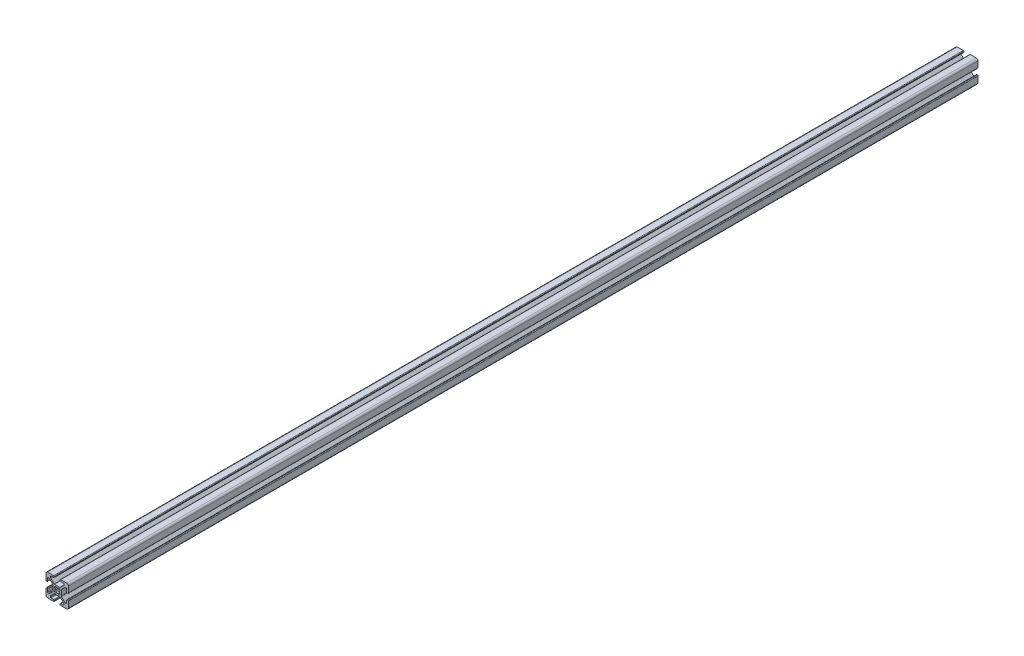
SolidWorks part; units mm, degrees
material "6063-T6"
ref_plane "Front Plane" through (0, 0, 0) normal (0, 0, 1) x (1, 0, 0)
ref_plane "Top Plane" through (0, 0, 0) normal (0, 1, 0) x (1, 0, 0)
ref_plane "Right Plane" through (0, 0, 0) normal (1, 0, 0) x (0, 0, -1)
sketch "Sketch1" plane through (0, 0, 0) normal (0, 0, 1) x (1, 0, 0)
  line L0 (9.492, 2.63) -> (9.008, 2.63)
  line L1 (8.5, 3.138) -> (8.5, 5.487)
  line L2 (10, 3.138) -> (10, 8.5)
  line L3 (3.655, -2.3839) -> (3.655, 2.3839)
  line L4 (7.2661, 5.995) -> (7.992, 5.995)
  line L5 (6.9069, 5.8462) -> (3.8038, 2.7431)
  line L6 (9.492, -2.63) -> (9.008, -2.63)
  line L7 (10, -3.138) -> (10, -8.5)
  line L8 (8.5, -3.138) -> (8.5, -5.487)
  line L9 (7.2661, -5.995) -> (7.992, -5.995)
  line L10 (6.9069, -5.8462) -> (3.8038, -2.7431)
  line L11 (2.1249, -2.3045) -> (2.3045, -2.1249)
  line L12 (-2.63, 9.492) -> (-2.63, 9.008)
  line L13 (-3.138, 10) -> (-8.5, 10)
  line L14 (-3.138, 8.5) -> (-5.487, 8.5)
  line L15 (2.3839, 3.655) -> (-2.3839, 3.655)
  line L16 (-5.995, 7.2661) -> (-5.995, 7.992)
  line L17 (-5.8462, 6.9069) -> (-2.7431, 3.8038)
  line L18 (2.63, 9.492) -> (2.63, 9.008)
  line L19 (3.138, 10) -> (8.5, 10)
  line L20 (3.138, 8.5) -> (5.487, 8.5)
  line L21 (5.995, 7.2661) -> (5.995, 7.992)
  line L22 (5.8462, 6.9069) -> (2.7431, 3.8038)
  line L23 (2.3045, 2.1249) -> (2.1249, 2.3045)
  line L24 (-9.492, -2.63) -> (-9.008, -2.63)
  line L25 (-10, -3.138) -> (-10, -8.5)
  line L26 (-8.5, -3.138) -> (-8.5, -5.487)
  line L27 (-3.655, 2.3839) -> (-3.655, -2.3839)
  line L28 (-7.2661, -5.995) -> (-7.992, -5.995)
  line L29 (-6.9069, -5.8462) -> (-3.8038, -2.7431)
  line L30 (-9.492, 2.63) -> (-9.008, 2.63)
  line L31 (-10, 3.138) -> (-10, 8.5)
  line L32 (-8.5, 3.138) -> (-8.5, 5.487)
  line L33 (-7.2661, 5.995) -> (-7.992, 5.995)
  line L34 (-6.9069, 5.8462) -> (-3.8038, 2.7431)
  line L35 (-2.1249, 2.3045) -> (-2.3045, 2.1249)
  line L36 (2.63, -9.492) -> (2.63, -9.008)
  line L37 (3.138, -10) -> (8.5, -10)
  line L38 (3.138, -8.5) -> (5.487, -8.5)
  line L39 (-2.3839, -3.655) -> (2.3839, -3.655)
  line L40 (5.995, -7.2661) -> (5.995, -7.992)
  line L41 (5.8462, -6.9069) -> (2.7431, -3.8038)
  line L42 (-2.63, -9.492) -> (-2.63, -9.008)
  line L43 (-3.138, -10) -> (-8.5, -10)
  line L44 (-3.138, -8.5) -> (-5.487, -8.5)
  line L45 (-5.995, -7.2661) -> (-5.995, -7.992)
  line L46 (-5.8462, -6.9069) -> (-2.7431, -3.8038)
  line L47 (-2.3045, -2.1249) -> (-2.1249, -2.3045)
  arc A0 (-0.804, -1.9351) -> (0.804, -1.9351) centre (0, 0) ccw
  arc A1 (8.5, 5.487) -> (7.992, 5.995) centre (7.992, 5.487) ccw
  arc A2 (7.2661, 5.995) -> (6.9069, 5.8462) centre (7.2661, 5.487) ccw
  arc A3 (3.8038, 2.7431) -> (3.655, 2.3839) centre (4.163, 2.3839) ccw
  arc A4 (3.655, -2.3839) -> (3.8038, -2.7431) centre (4.163, -2.3839) ccw
  arc A5 (6.9069, -5.8462) -> (7.2661, -5.995) centre (7.2661, -5.487) ccw
  arc A6 (7.992, -5.995) -> (8.5, -5.487) centre (7.992, -5.487) ccw
  arc A7 (9.008, -2.63) -> (8.5, -3.138) centre (9.008, -3.138) ccw
  arc A8 (10, -3.138) -> (9.492, -2.63) centre (9.492, -3.138) ccw
  arc A9 (9.492, 2.63) -> (10, 3.138) centre (9.492, 3.138) ccw
  arc A10 (8.5, 3.138) -> (9.008, 2.63) centre (9.008, 3.138) ccw
  arc A11 (0.804, -1.9351) -> (2.1249, -2.3045) centre (1.5684, -1.748) ccw
  arc A12 (2.3045, -2.1249) -> (1.9351, -0.804) centre (1.748, -1.5684) ccw
  arc A13 (-2.63, 9.492) -> (-3.138, 10) centre (-3.138, 9.492) ccw
  arc A14 (-3.138, 8.5) -> (-2.63, 9.008) centre (-3.138, 9.008) ccw
  arc A15 (1.9351, -0.804) -> (1.9351, 0.804) centre (0, 0) ccw
  arc A16 (-2.7431, 3.8038) -> (-2.3839, 3.655) centre (-2.3839, 4.163) ccw
  arc A17 (-5.487, 8.5) -> (-5.995, 7.992) centre (-5.487, 7.992) ccw
  arc A18 (-5.995, 7.2661) -> (-5.8462, 6.9069) centre (-5.487, 7.2661) ccw
  arc A19 (2.63, 9.008) -> (3.138, 8.5) centre (3.138, 9.008) ccw
  arc A20 (3.138, 10) -> (2.63, 9.492) centre (3.138, 9.492) ccw
  arc A21 (5.995, 7.992) -> (5.487, 8.5) centre (5.487, 7.992) ccw
  arc A22 (5.8462, 6.9069) -> (5.995, 7.2661) centre (5.487, 7.2661) ccw
  arc A23 (2.3839, 3.655) -> (2.7431, 3.8038) centre (2.3839, 4.163) ccw
  arc A24 (1.9351, 0.804) -> (2.3045, 2.1249) centre (1.748, 1.5684) ccw
  arc A25 (2.1249, 2.3045) -> (0.804, 1.9351) centre (1.5684, 1.748) ccw
  arc A26 (-9.492, -2.63) -> (-10, -3.138) centre (-9.492, -3.138) ccw
  arc A27 (-8.5, -3.138) -> (-9.008, -2.63) centre (-9.008, -3.138) ccw
  arc A28 (0.804, 1.9351) -> (-0.804, 1.9351) centre (0, 0) ccw
  arc A29 (-3.8038, -2.7431) -> (-3.655, -2.3839) centre (-4.163, -2.3839) ccw
  arc A30 (-8.5, -5.487) -> (-7.992, -5.995) centre (-7.992, -5.487) ccw
  arc A31 (-7.2661, -5.995) -> (-6.9069, -5.8462) centre (-7.2661, -5.487) ccw
  arc A32 (-9.008, 2.63) -> (-8.5, 3.138) centre (-9.008, 3.138) ccw
  arc A33 (-10, 3.138) -> (-9.492, 2.63) centre (-9.492, 3.138) ccw
  arc A34 (-7.992, 5.995) -> (-8.5, 5.487) centre (-7.992, 5.487) ccw
  arc A35 (-6.9069, 5.8462) -> (-7.2661, 5.995) centre (-7.2661, 5.487) ccw
  arc A36 (-3.655, 2.3839) -> (-3.8038, 2.7431) centre (-4.163, 2.3839) ccw
  arc A37 (-0.804, 1.9351) -> (-2.1249, 2.3045) centre (-1.5684, 1.748) ccw
  arc A38 (-2.3045, 2.1249) -> (-1.9351, 0.804) centre (-1.748, 1.5684) ccw
  arc A39 (2.63, -9.492) -> (3.138, -10) centre (3.138, -9.492) ccw
  arc A40 (3.138, -8.5) -> (2.63, -9.008) centre (3.138, -9.008) ccw
  arc A41 (-1.9351, 0.804) -> (-1.9351, -0.804) centre (0, 0) ccw
  arc A42 (2.7431, -3.8038) -> (2.3839, -3.655) centre (2.3839, -4.163) ccw
  arc A43 (5.487, -8.5) -> (5.995, -7.992) centre (5.487, -7.992) ccw
  arc A44 (5.995, -7.2661) -> (5.8462, -6.9069) centre (5.487, -7.2661) ccw
  arc A45 (-2.63, -9.008) -> (-3.138, -8.5) centre (-3.138, -9.008) ccw
  arc A46 (-3.138, -10) -> (-2.63, -9.492) centre (-3.138, -9.492) ccw
  arc A47 (-5.995, -7.992) -> (-5.487, -8.5) centre (-5.487, -7.992) ccw
  arc A48 (-5.8462, -6.9069) -> (-5.995, -7.2661) centre (-5.487, -7.2661) ccw
  arc A49 (-2.3839, -3.655) -> (-2.7431, -3.8038) centre (-2.3839, -4.163) ccw
  arc A50 (-1.9351, -0.804) -> (-2.3045, -2.1249) centre (-1.748, -1.5684) ccw
  arc A51 (-2.1249, -2.3045) -> (-0.804, -1.9351) centre (-1.5684, -1.748) ccw
  arc A52 (10, 8.5) -> (8.5, 10) centre (8.5, 8.5) ccw
  arc A53 (8.5, -10) -> (10, -8.5) centre (8.5, -8.5) ccw
  arc A54 (-10, -8.5) -> (-8.5, -10) centre (-8.5, -8.5) ccw
  arc A55 (-8.5, 10) -> (-10, 8.5) centre (-8.5, 8.5) ccw
extrude "Extrude1" add sketch "Sketch1" along normal mid plane 812.8
